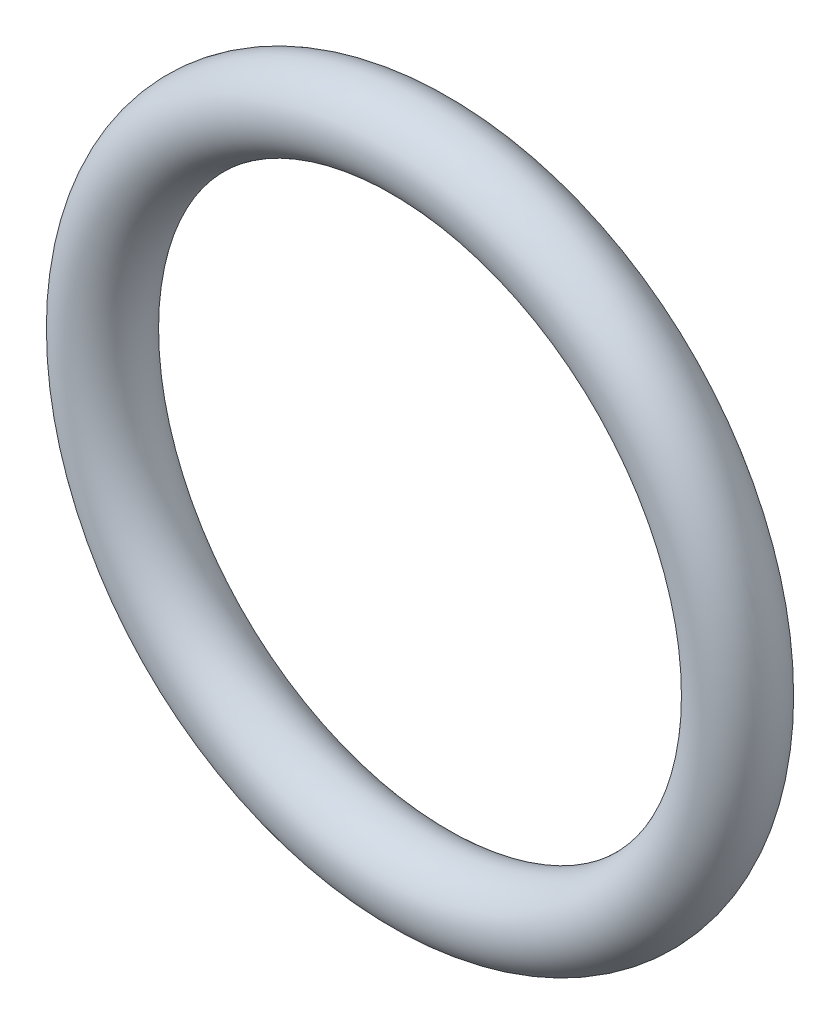
SolidWorks part; units mm, degrees
ref_plane "Front" through (0, 0, 0) normal (0, 0, 1) x (1, 0, 0)
ref_plane "Top" through (0, 0, 0) normal (0, 1, 0) x (1, 0, 0)
ref_plane "Right" through (0, 0, 0) normal (1, 0, 0) x (0, 0, -1)
sketch "Sketch1" plane through (0, 0, 0) normal (1, 0, 0) x (0, -1, 0)
  line L0 (0, -0.5) -> (0, 0.5) construction
  line L2 (-54.1896, 0) -> (54.1896, 0) construction
  line L3 (-3.5, 0) -> (3.5, 0) construction
  circle A0 centre (4, 0) radius 0.5
  point P9 (3.5, 0)
  point P10 (4.5, 0)
  point P13 (4, 0.5)
  point P14 (4, -0.5)
  dimension "Width" = 1
  dimension "ID" = 7
revolve "Revolve1" add sketch "Sketch1" angle 360 about L0
sketch "Sketch2" plane through (0, 0, 0) normal (0, 0, 1) x (1, 0, 0)
  circle A0 centre (0, 0) radius 2.334
